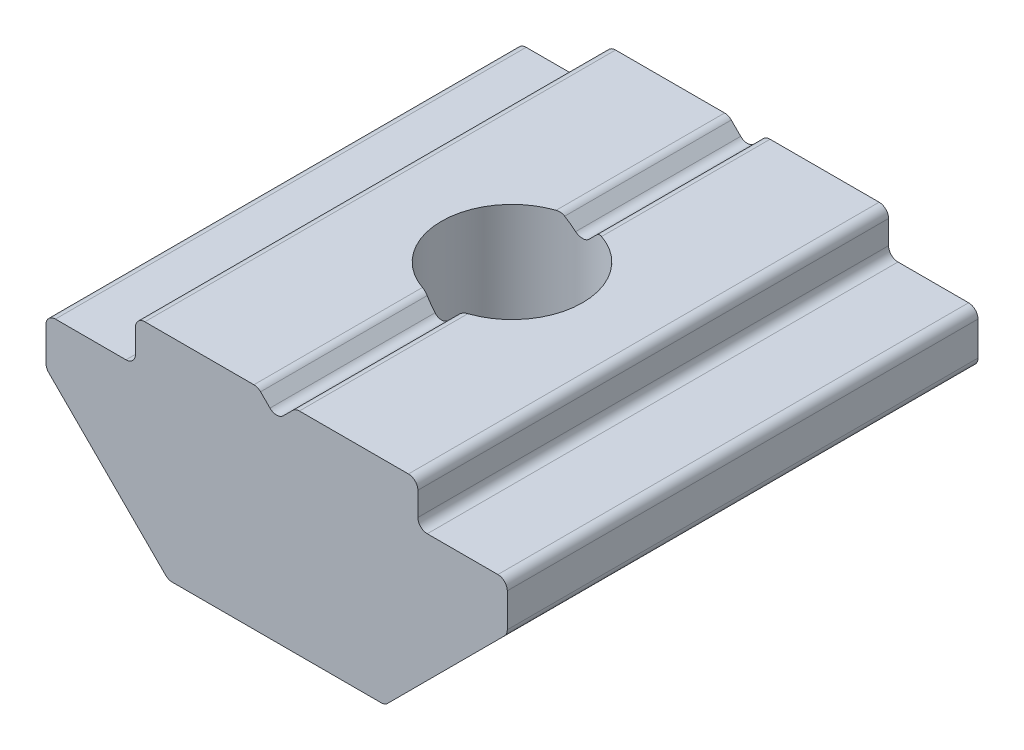
SolidWorks part; units mm, degrees
ref_plane "Front Plane" through (0, 0, 0) normal (0, 0, 1) x (1, 0, 0)
ref_plane "Top Plane" through (0, 0, 0) normal (0, 1, 0) x (1, 0, 0)
ref_plane "Right Plane" through (0, 0, 0) normal (1, 0, 0) x (0, 0, -1)
ref_plane "Plane1" through (0, 0, 5) normal (0, 0, 1) x (1, 0, 0)
sketch "Sketch1" plane through (0, 0, 5) normal (0, 0, 1) x (1, 0, 0)
  line L0 (4.9, -1) -> (4.9, 0.9)
  line L1 (4.9, 0.9) -> (-4.9, 0.9)
  line L2 (-4.9, 0.9) -> (-4.9, -1)
  line L3 (-4.9, -1) -> (-2.3, -3.6)
  line L4 (-2.3, -3.6) -> (2.3, -3.6)
  line L5 (2.3, -3.6) -> (4.9, -1)
extrude "Extrude Body" add sketch "Sketch1" against normal blind 10
sketch "Sketch2" plane through (0, 0, -5) normal (0, 0, -1) x (-1, 0, 0)
  line L0 (4.9, 0.9) -> (3, 0.9)
  line L1 (3, 0.9) -> (3, 0)
  line L2 (3, 0) -> (4.9, 0)
  line L3 (4.9, 0) -> (4.9, 0.9)
extrude "Cut-Extrude1" cut sketch "Sketch2" against normal through all
sketch "Sketch3" plane through (0, 0, -5) normal (0, 0, -1) x (-1, 0, 0)
  line L0 (-4.9, 0) -> (-3, 0)
  line L1 (-3, 0) -> (-3, 0.9)
  line L2 (-3, 0.9) -> (-4.9, 0.9)
  line L3 (-4.9, 0.9) -> (-4.9, 0)
extrude "Cut-Extrude2" cut sketch "Sketch3" against normal through all
sketch "Sketch4" plane through (0, 0, -5) normal (0, 0, -1) x (-1, 0, 0)
  line L0 (0.4, 0.9) -> (-0.4, 0.9)
  line L1 (-0.4, 0.9) -> (0, 0.5)
  line L2 (0, 0.5) -> (0.4, 0.9)
extrude "Cut-Extrude3" cut sketch "Sketch4" against normal through all
hole_wizard "Hole Revolve" positions "Hole Locating Sketch" profile "Hole Cut Out Sketch" hole size "Ø4.2" standard "ANSI Metric" end condition through all
sketch "Hole Locating Sketch" plane through (0, -3.6, 0) normal (0, -1, 0) x (-1, 0, 0)
  point P0 (0, 0)
sketch "Hole Cut Out Sketch" plane through (0, -3.6, 0) normal (1, 0, 0) x (0, 0, -1)
  line L0 (0, 0) -> (0, 4.5)
  line L1 (0, 4.5) -> (1.5, 4.5)
  line L2 (1.5, 4.5) -> (1.5, 0)
  line L5 (1.5, 0) -> (0, 0)
  line L11 (0, -6.35) -> (0, 107.95) construction
  dimension "Thru Hole Dia." = 3
  dimension "Thru Hole Depth" = 4.5
fillet "Edge Fillets" radius 0.2 16 edges at (4.9, 0, 0) (3, 0, 0) (-4.9, -1, 0) (3, 0.9, 0) (-3, 0, 0) (0.4, 0.9, -3.2228) (0, 0.5, 3.25) (-0.4, 0.9, -3.2228) (4.9, -1, 0) (-3, 0.9, 0) (0, 0.5, -3.25) (-0.4, 0.9, 3.2228) (-4.9, 0, 0) (-2.3, -3.6, 0) (0.4, 0.9, 3.2228) (2.3, -3.6, 0)
